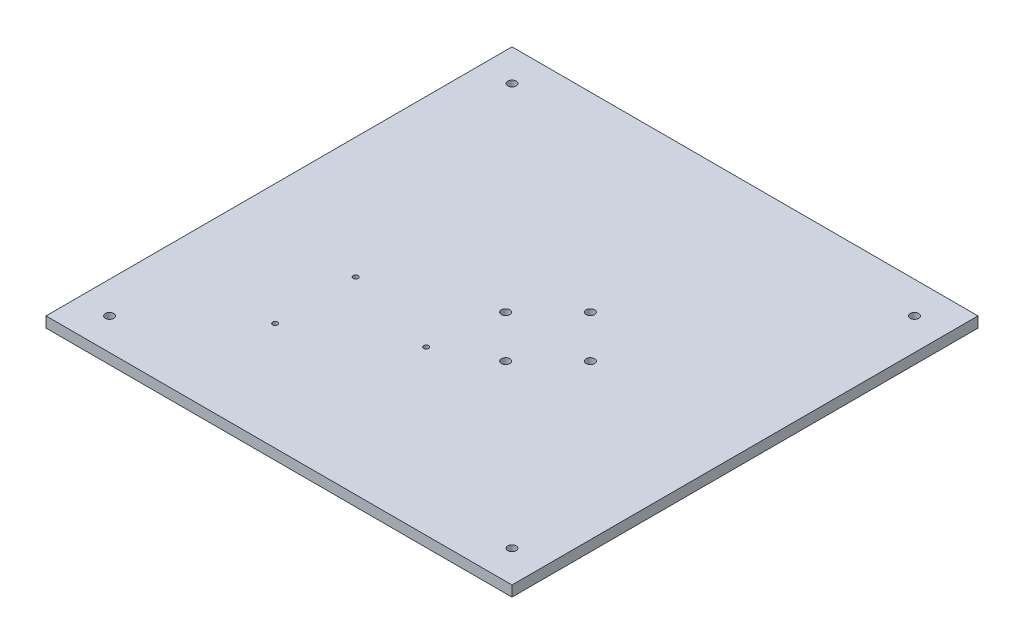
SolidWorks part; units mm, degrees
ref_plane "Front Plane" through (0, 0, 0) normal (0, 0, 1) x (1, 0, 0)
ref_plane "Top Plane" through (0, 0, 0) normal (0, 1, 0) x (1, 0, 0)
ref_plane "Right Plane" through (0, 0, 0) normal (1, 0, 0) x (0, 0, -1)
sketch "Sketch1" plane through (0, 0, 0) normal (0, 1, 0) x (1, 0, 0)
  line L1 (-126.5931, 154.4053) -> (152.8069, 154.4053)
  line L2 (-126.5931, 154.4053) -> (-126.5931, -124.9947)
  line L3 (-126.5931, -124.9947) -> (152.8069, -124.9947)
  line L4 (152.8069, 154.4053) -> (152.8069, -124.9947)
  dimension "D1" = 279.4
  dimension "D2" = 279.4
extrude "base_extrusion" add sketch "Sketch1" along normal blind 6.35
sketch "Sketch2" plane through (0, 6.35, 0) normal (0, 1, 0) x (1, 0, 0)
  line L0 (-107.5431, 154.4053) -> (-107.5431, -124.9947) construction
  line L1 (152.8069, 154.4053) -> (-126.5931, 154.4053) construction
  line L2 (-126.5931, -124.9947) -> (152.8069, -124.9947) construction
  line L3 (-173.0492, 135.3553) -> (179.0204, 135.3553) construction
  line L4 (-170.255, -105.9447) -> (184.1431, -105.9447) construction
  line L5 (133.7569, 179.548) -> (133.7569, -168.3303) construction
  line L6 (-126.5931, 154.4053) -> (-126.5931, -124.9947) construction
  line L7 (152.8069, -124.9947) -> (152.8069, 154.4053) construction
  circle A0 centre (-107.5431, 135.3553) radius 2.54
  circle A2 centre (133.7569, 135.3553) radius 2.54
  circle A3 centre (133.7569, -105.9447) radius 2.54
  circle A4 centre (-107.5431, -105.9447) radius 2.54
  point P22 (-107.5431, -105.9447)
  dimension "D5" = 5.08
  dimension "D6" = 5.08
  dimension "D7" = 5.08
  dimension "D8" = 5.08
  dimension "D1" = 19.05
  dimension "D2" = 19.05
  dimension "D3" = 19.05
  dimension "D4" = 19.05
extrude "construction_holes" cut sketch "Sketch2" against normal blind 6.35
sketch "Sketch3" plane through (0, 6.35, 0) normal (0, 1, 0) x (1, 0, 0)
  line L0 (-126.5931, -124.9947) -> (152.8069, -124.9947) construction
  line L1 (-78.9431, -1.0947) -> (3.5569, -1.0947)
  line L2 (-78.9431, -1.0947) -> (-78.9431, -71.0947)
  line L3 (-78.9431, -71.0947) -> (3.5569, -71.0947)
  line L4 (3.5569, -1.0947) -> (3.5569, -71.0947)
  line L5 (-126.5931, 154.4053) -> (-126.5931, -124.9947) construction
  circle A0 centre (3.5569, -27.2047) radius 1.5
  circle A1 centre (-53.9831, -60.2247) radius 1.5
  circle A2 centre (-53.9831, -11.9647) radius 1.5
  point P4 (-78.9431, -36.0947)
  point P7 (-37.6931, -1.0947)
  point P16 (0, 0)
  point P17 (-3.1831, 30.2448)
  dimension "D6" = 3
  dimension "D7" = 57.54
  dimension "D9" = 3
  dimension "D10" = 3
  dimension "D1" = 70
  dimension "D2" = 82.5
  dimension "D3" = 88.9
  dimension "D4" = 88.9
  dimension "D5" = 43.89
  dimension "D8" = 10.87
  dimension "D11" = 10.87
  dimension "D12" = 57.54
extrude "board holes" cut sketch "Sketch3" against normal blind 127 contours A2 | A1 | A0
sketch "Sketch4" plane through (0, 6.35, 0) normal (0, 1, 0) x (1, 0, 0)
  line L0 (-126.5931, 14.7053) -> (152.8069, 14.7053) construction
  line L1 (-126.5931, 154.4053) -> (-126.5931, -124.9947) construction
  line L2 (152.8069, -124.9947) -> (152.8069, 154.4053) construction
  line L3 (13.1069, 154.4053) -> (13.1069, -124.9947) construction
  line L4 (152.8069, 154.4053) -> (-126.5931, 154.4053) construction
  line L5 (-126.5931, -124.9947) -> (152.8069, -124.9947) construction
  line L7 (15.6469, 33.7553) -> (53.7469, 33.7553) construction
  line L8 (15.6469, 33.7553) -> (15.6469, -4.3447)
  line L9 (15.6469, -4.3447) -> (53.7469, -4.3447)
  line L10 (53.7469, 33.7553) -> (53.7469, -4.3447)
  circle A0 centre (34.6969, -10.6947) radius 2.54
  circle A1 centre (60.0969, 14.7053) radius 2.54
  circle A2 centre (34.6969, 40.1053) radius 2.54
  circle A3 centre (9.2969, 14.7053) radius 2.54
  point P16 (34.6969, -4.3447)
  point P25 (0, 0)
  point P26 (0, 0)
  point P27 (0, 0)
  point P28 (34.6969, 33.7553)
  dimension "D5" = 5.08
  dimension "D6" = 5.08
  dimension "D7" = 5.08
  dimension "D8" = 5.08
  dimension "D1" = 38.1
  dimension "D2" = 38.1
  dimension "D3" = 21.59
  dimension "D4" = 19.05
  dimension "D9" = 25.4
  dimension "D10" = 25.4
  dimension "D11" = 19.05
  dimension "D12" = 25.4
  dimension "D13" = 19.05
  dimension "D14" = 25.4
extrude "motor holes" cut sketch "Sketch4" against normal blind 36.576 contours A2 | A1 | A0 | A3
